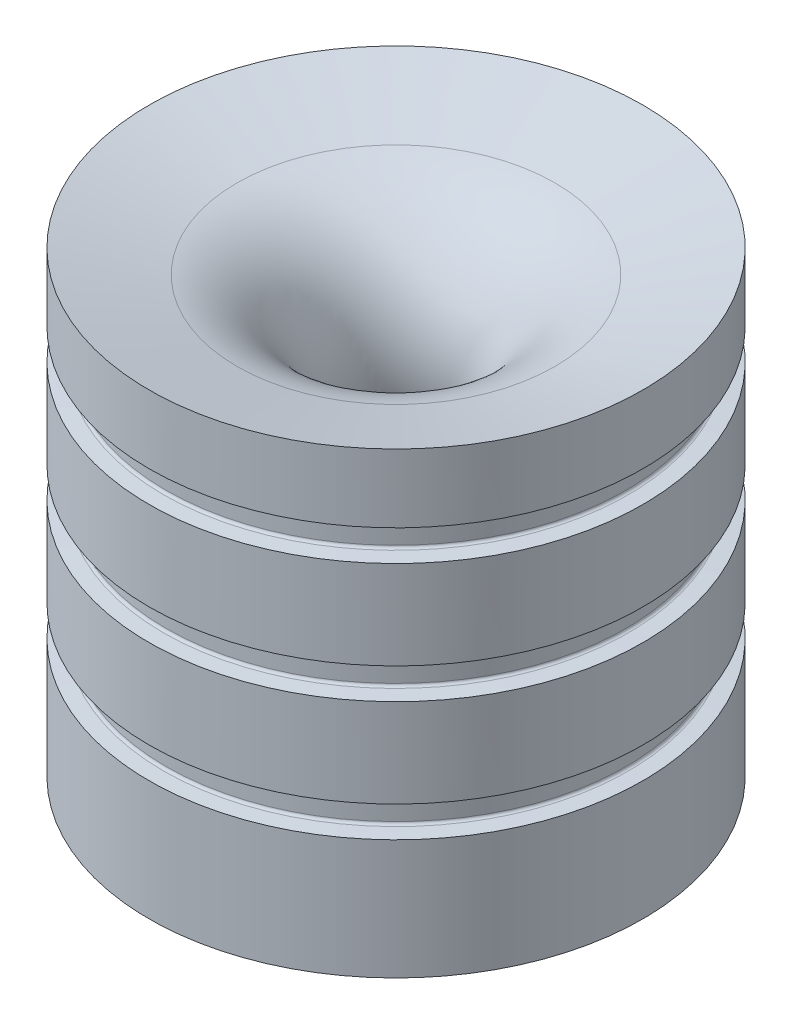
SolidWorks part; units mm, degrees
material "C (Graphite)"
ref_plane "Front Plane" through (0, 0, 0) normal (0, 0, 1) x (1, 0, 0)
ref_plane "Top Plane" through (0, 0, 0) normal (0, 1, 0) x (1, 0, 0)
ref_plane "Right Plane" through (0, 0, 0) normal (1, 0, 0) x (0, 0, -1)
sketch "Sketch1" plane through (0, 0, 0) normal (0, 0, 1) x (1, 0, 0)
  line L0 (0, -55) -> (0, 55) construction
  line L1 (41.275, 76.5908) -> (41.275, 0)
  line L2 (41.275, 76.5908) -> (26.581, 72.6535)
  line L3 (41.275, 0) -> (23.2724, 0)
  line L4 (23.2724, 0) -> (11.0246, 45.7092)
  line L5 (0, 11.2039) -> (0, 47.7588) construction
  arc A0 (11.0246, 45.7092) -> (26.581, 72.6535) centre (32.275, 51.4032) cw
  dimension "D6" = 32.275
  dimension "D3" = 22
  dimension "D1" = 41.275
  dimension "D2" = 23.2724
  dimension "D4" = 105
  dimension "D5" = 75
revolve "Revolve1" add sketch "Sketch1" angle 360 about L5
ref_plane "Plane1" through (0, 11.2039, 0) normal (-1, 0, 0) x (0, 0, -1)
sketch "Sketch3" plane through (0, 11.2039, 0) normal (-1, 0, 0) x (0, 0, -1)
  line L0 (38.8614, -9.0151) -> (41.3639, -8.7961)
  line L1 (41.3639, -8.7961) -> (41.3639, -13.9838)
  line L2 (41.3639, -13.9838) -> (38.8614, -13.7649)
  line L3 (38.4556, -13.322) -> (38.4556, -9.4579)
  line L4 (0, 50) -> (0, -50) construction
  line L5 (41.275, 11.2039) -> (-41.275, 11.2039) construction
  arc A0 (38.8614, -13.7649) -> (38.4556, -13.322) centre (38.9001, -13.322) cw
  arc A1 (38.4556, -9.4579) -> (38.8614, -9.0151) centre (38.9001, -9.4579) cw
  dimension "D1" = 20
revolve "Groove for AS 568-234, O-Ring1" cut sketch "Sketch3"
pattern_linear "LPattern1" count 3 spacing 20 along (0, 1, 0) of "Groove for AS 568-234, O-Ring1"
